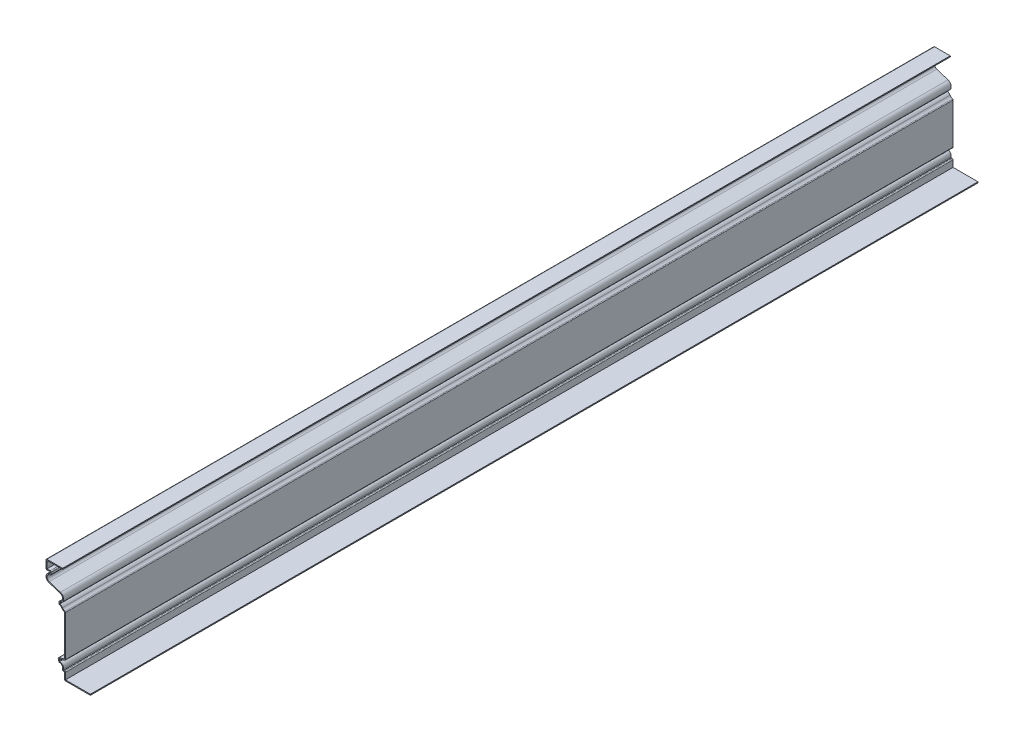
SolidWorks part; units mm, degrees
ref_plane "Front Plane" through (0, 0, 0) normal (0, 0, 1) x (1, 0, 0)
ref_plane "Top Plane" through (0, 0, 0) normal (0, 1, 0) x (1, 0, 0)
ref_plane "Right Plane" through (0, 0, 0) normal (1, 0, 0) x (0, 0, -1)
sketch "Sketch1" plane through (0, 0, 0) normal (0, 0, 1) x (1, 0, 0)
  line L0 (0, 0) -> (-44.45, 0)
  line L1 (-44.45, 0) -> (-44.45, 12.7)
  line L2 (-44.45, 12.7) -> (-47.625, 12.7)
  line L3 (-53.975, 22.225) -> (-55.5625, 28.575)
  line L4 (-55.5625, 28.575) -> (-44.45, 31.75)
  line L5 (-44.45, 31.75) -> (-44.45, 101.6)
  line L6 (-47.625, 12.7) -> (-47.625, 16.7257)
  line L7 (-53.975, 108.7438) -> (-53.975, 113.5063)
  line L8 (-52.0236, 125.899) -> (-71.2515, 132.1082)
  line L9 (-69.0563, 146.05) -> (-69.0563, 149.225)
  line L10 (-69.0563, 149.225) -> (-76.2, 149.225)
  line L11 (-76.2, 149.225) -> (-76.2, 165.1)
  line L12 (-76.2, 165.1) -> (-47.625, 165.1)
  arc A0 (-47.625, 16.7257) -> (-53.975, 22.225) centre (-53.1812, 16.7257) ccw
  arc A1 (-44.45, 101.6) -> (-49.268, 105.3617) centre (-40.4895, 111.6389) cw
  arc A2 (-49.268, 105.3617) -> (-53.975, 108.7438) centre (-56.6075, 100.1134) ccw
  arc A3 (-53.975, 113.5063) -> (-52.0236, 125.899) centre (-53.975, 119.8563) ccw
  arc A4 (-71.2515, 132.1082) -> (-69.0563, 146.05) centre (-69.0563, 138.9062) cw
  point P19 (-48.2545, 105.3885)
  point P26 (-49.8625, 105.0644)
  point P27 (-49.268, 105.3617)
  point P28 (-67.4099, 132.3083)
  dimension "D4" = 5.5562
  dimension "D13" = 9.0229
  dimension "D14" = 10.7919
  dimension "D16" = 6.35
  dimension "D19" = 7.1437
  dimension "D1" = 44.45
  dimension "D2" = 12.7
  dimension "D3" = 3.175
  dimension "D5" = 6.35
  dimension "D6" = 9.525
  dimension "D7" = 1.5875
  dimension "D8" = 11.1125
  dimension "D9" = 3.175
  dimension "D10" = 69.85
  dimension "D11" = 9.525
  dimension "D12" = 7.1437
  dimension "D15" = 4.818
  dimension "D17" = 4.7625
  dimension "D18" = 19.05
  dimension "D20" = 3.175
  dimension "D21" = 15.875
  dimension "D22" = 28.575
  dimension "D23" = 165.1
  dimension "D24" = 76.2
extrude "Extrude-Thin1" add sketch "Sketch1" against normal blind 1524 thin
fillet "Fillet1" radius 1.651 13 edges at (-44.45, 0, -762) (-42.799, 14.351, -762) (-47.625, 12.7, -762) (-53.975, 22.225, -762) (-55.5625, 28.575, -762) (-42.799, 30.5046, -762) (-42.799, 102.7946, -762) (-53.975, 108.7438, -762) (-53.975, 113.5063, -762) (-67.4052, 144.145, -762) (-67.4052, 150.876, -762) (-76.2, 149.225, -762) (-76.2, 165.1, -762)
